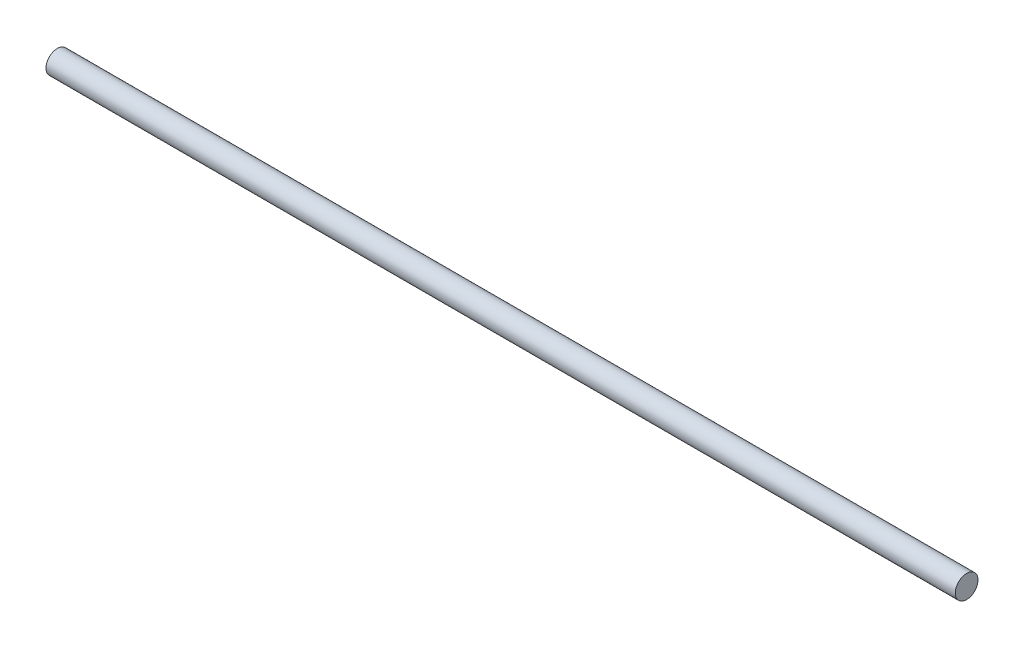
SolidWorks part; units mm, degrees
ref_plane "Front" through (0, 0, 0) normal (0, 0, 1) x (1, 0, 0)
ref_plane "Top" through (0, 0, 0) normal (0, 1, 0) x (1, 0, 0)
ref_plane "Right" through (0, 0, 0) normal (1, 0, 0) x (0, 0, -1)
sketch "Sketch1" plane through (0, 0, 0) normal (1, 0, 0) x (0, 0, -1)
  circle A0 centre (0, 0) radius 6.35
  dimension "D1" = 12.7
extrude "Boss-Extrude1" add sketch "Sketch1" along normal blind 508
